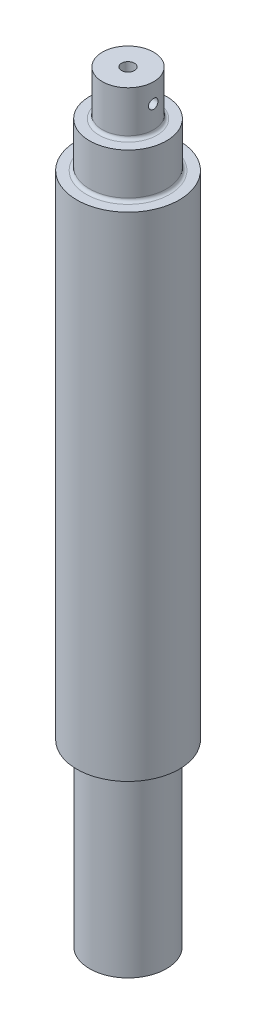
SolidWorks part; units mm, degrees
material "ASTM A36 Steel"
ref_plane "Front Plane" through (0, 0, 0) normal (0, 0, 1) x (1, 0, 0)
ref_plane "Top Plane" through (0, 0, 0) normal (0, 1, 0) x (1, 0, 0)
ref_plane "Right Plane" through (0, 0, 0) normal (1, 0, 0) x (0, 0, -1)
sketch "Sketch1" plane through (0, 0, 0) normal (0, 0, 1) x (1, 0, 0)
  line L0 (0, -122.1935) -> (0, 97.1905) construction
  line L1 (0, 83.3438) -> (-6.35, 83.3438)
  line L2 (-6.35, 83.3438) -> (-6.35, 73.025)
  line L3 (-7.1437, 72.2313) -> (-9.5377, 72.2313)
  line L4 (-9.5377, 72.2313) -> (-9.5377, 61.9125)
  line L6 (-10.3314, 61.1187) -> (-12.7, 61.1187)
  line L8 (-12.7, 61.1187) -> (-12.7, 0)
  line L9 (55, 0) -> (-55, 0) construction
  line L10 (-12.7, 0) -> (-12.7, -61.1188)
  line L11 (-12.7, -61.1188) -> (-10.306, -61.1187)
  line L12 (-9.5123, -61.9125) -> (-9.5123, -105.5688)
  line L13 (-9.5123, -105.5688) -> (0, -105.5688)
  line L14 (0, 83.3438) -> (0, -105.5688)
  arc A0 (-6.35, 73.025) -> (-7.1437, 72.2313) centre (-7.1437, 73.025) cw
  arc A1 (-9.5377, 61.9125) -> (-10.3314, 61.1187) centre (-10.3314, 61.9125) cw
  arc A2 (-10.306, -61.1187) -> (-9.5123, -61.9125) centre (-10.306, -61.9125) cw
  dimension "D2" = 0.7937
  dimension "D1" = 12.7
  dimension "D3" = 19.0754
  dimension "D4" = 25.4
  dimension "D5" = 11.1125
  dimension "D6" = 11.1125
  dimension "D7" = 122.2375
  dimension "D8" = 19.0246
  dimension "D9" = 44.45
revolve "Revolve1" add sketch "Sketch1" angle 360 mid plane about L0
sketch "Sketch2" plane through (0, 83.3438, 0) normal (0, 1, 0) x (1, 0, 0)
  circle A0 centre (0, 0) radius 1.6002
  dimension "D1" = 3.2004
extrude "Cut-Extrude1" cut sketch "Sketch2" against normal blind 12.7
sketch "Sketch3" plane through (0, 0, 0) normal (1, 0, 0) x (0, 0, -1)
  line L0 (9.5377, 72.2313) -> (-9.5377, 72.2313) construction
  line L1 (9.5377, 72.2313) -> (-9.5377, 72.2313) construction
  line L2 (0, 55) -> (0, -55) construction
  circle A0 centre (0, 78.5812) radius 1.1811
  dimension "D1" = 2.3622
  dimension "D2" = 6.35
extrude "Cut-Extrude2" cut sketch "Sketch3" against normal mid plane 25.4
